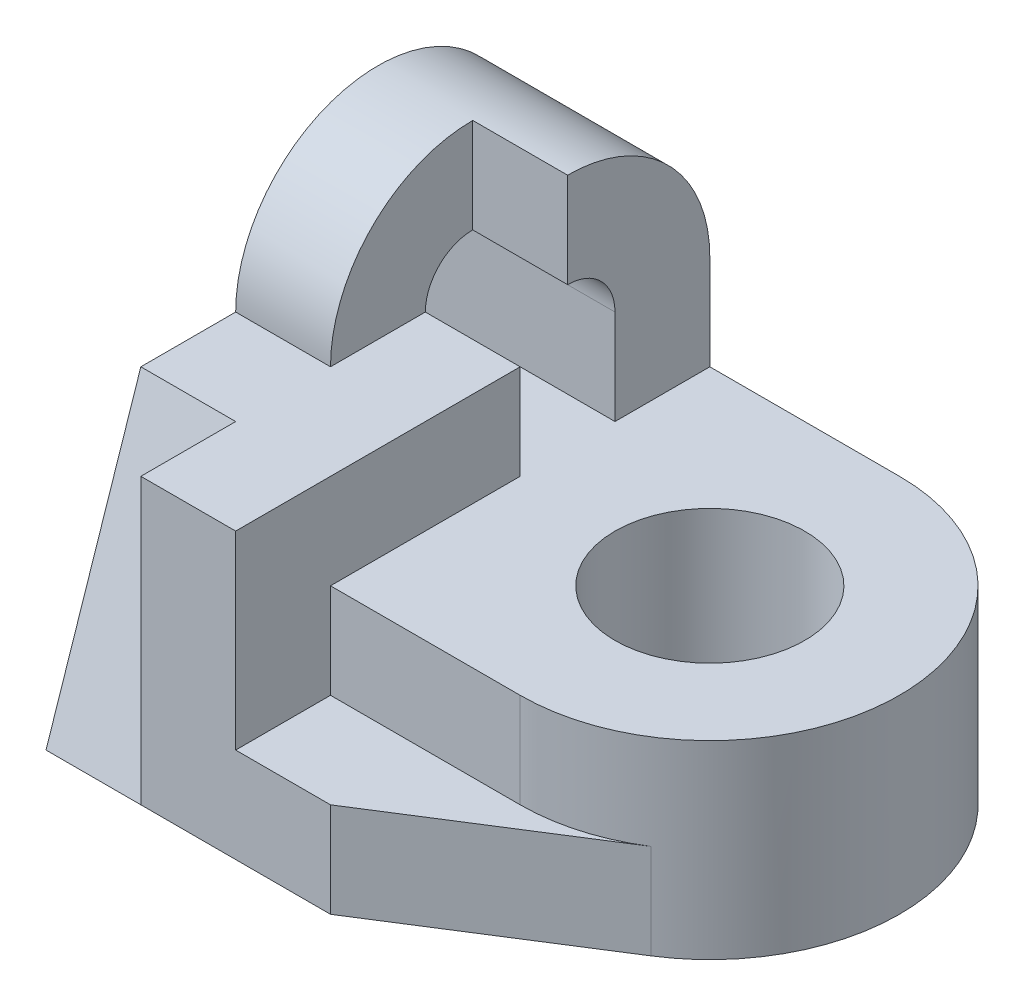
SolidWorks part; units mm, degrees
ref_plane "Front Plane" through (0, 0, 0) normal (0, 0, 1) x (1, 0, 0)
ref_plane "Top Plane" through (0, 0, 0) normal (0, 1, 0) x (1, 0, 0)
ref_plane "Right Plane" through (0, 0, 0) normal (1, 0, 0) x (0, 0, -1)
sketch "Sketch1" plane through (0, 0, 0) normal (0, 0, 1) x (1, 0, 0)
  line L1 (2, -1) -> (-2, -1)
  line L2 (2, -1) -> (2, 1)
  line L3 (2, 1) -> (-2, 1)
  line L4 (-2, -1) -> (-2, 1)
  line L5 (2, -1) -> (-2, 1) construction
  line L6 (2, 1) -> (-2, -1) construction
  point P0 (0, 0)
  dimension "D1" = 4
  dimension "D2" = 2
extrude "Boss-Extrude1" add sketch "Sketch1" along normal blind 4
sketch "Sketch2" plane through (0, 1, 0) normal (0, 1, 0) x (1, 0, 0)
  line L0 (2, 0) -> (2, -4)
  arc A0 (2, 0) -> (2, -4) centre (2, -2) cw
  dimension "D1" = 2
extrude "Boss-Extrude2" add sketch "Sketch2" against normal blind 2
sketch "Sketch3" plane through (0, 1, 0) normal (0, 1, 0) x (1, 0, 0)
  circle A0 centre (2, -2) radius 1
  dimension "D1" = 2
extrude "Cut-Extrude1" cut sketch "Sketch3" against normal through all
sketch "Sketch4" plane through (-2, 0, 0) normal (-1, 0, 0) x (0, 0, 1)
  line L0 (0, 1) -> (0, 2)
  line L1 (1, 1) -> (1, 2)
  line L2 (4, 1) -> (0, 1) construction
  line L3 (3, 1) -> (3, 2)
  line L4 (1, 1) -> (0, 1)
  line L5 (2, 1) -> (2, 2)
  line L6 (3, 1) -> (2, 1)
  arc A0 (0, 2) -> (3, 2) centre (1.5, 2) cw
  arc A1 (1, 2) -> (2, 2) centre (1.5, 2) cw
  dimension "D1" = 1
  dimension "D2" = 1
  dimension "D3" = 1
  dimension "D4" = 1
  dimension "D5" = 1
  dimension "D6" = 2
  dimension "D7" = 1
extrude "Boss-Extrude4" add sketch "Sketch4" against normal blind 2
sketch "Sketch7" plane through (0, 0, 0) normal (1, 0, 0) x (0, 0, -1)
  line L0 (-1.5, 2.5) -> (-1.5, 3.5)
  line L1 (-2, 2) -> (-3, 2)
  arc A0 (-1, 2) -> (-2, 2) centre (-1.5, 2) ccw construction
  arc A1 (0, 2) -> (-3, 2) centre (-1.5, 2) ccw construction
  arc A2 (-1.5, 2.5) -> (-2, 2) centre (-1.5, 2) ccw
  arc A3 (-3, 2) -> (-1.5, 3.5) centre (-1.5, 2) cw
extrude "Cut-Extrude2" cut sketch "Sketch7" against normal blind 1
sketch "Sketch8" plane through (-2, 0, 0) normal (-1, 0, 0) x (0, 0, 1)
  line L0 (4, 1) -> (5, 1)
  line L1 (5, 1) -> (5, -1)
  line L2 (5, -1) -> (4, -1)
  line L3 (4, -1) -> (4, 1)
  dimension "D1" = 1
extrude "Boss-Extrude5" add sketch "Sketch8" against normal blind 2
sketch "Sketch9" plane through (-2, 0, 0) normal (-1, 0, 0) x (0, 0, 1)
  line L0 (5, 1) -> (4, 1)
  line L1 (5, 1) -> (3, 1) construction
  line L2 (4, 1) -> (5, -1)
  line L3 (5, -1) -> (5, 1)
extrude "Cut-Extrude3" cut sketch "Sketch9" against normal blind 1
sketch "Sketch10" plane through (0, -1, 0) normal (0, -1, 0) x (-1, 0, 0)
  line L0 (0, -5) -> (-1, -5)
  line L1 (-1, -5) -> (-3.0697, -3.6899)
  line L2 (0, -5) -> (0, -4)
  line L3 (0, -4) -> (-2, -4)
  arc A0 (-2, 0) -> (-2, -4) centre (-2, -2) ccw construction
  arc A1 (-3.0697, -3.6899) -> (-2, -4) centre (-2, -2) ccw
  dimension "D1" = 1
extrude "Boss-Extrude6" add sketch "Sketch10" against normal blind 1
sketch "Sketch11" plane through (0, 1, 0) normal (0, 1, 0) x (1, 0, 0)
  line L0 (0, -3) -> (0, -5)
  line L1 (0, -5) -> (-1, -5)
  line L2 (-1, -5) -> (-1, -4)
  line L3 (-1, -4) -> (-2, -4)
  line L4 (-2, -4) -> (-2, -3)
  line L5 (-2, -3) -> (0, -3)
extrude "Boss-Extrude7" add sketch "Sketch11" along normal blind 1
sketch "Sketch12" plane through (-1, 0, 0) normal (-1, 0, 0) x (0, 0, 1)
  line L0 (4, 2) -> (5, -1)
  line L1 (5, -1) -> (4, 1)
  line L2 (4, 1) -> (4, 2)
extrude "Boss-Extrude8" add sketch "Sketch12" along normal blind 1
